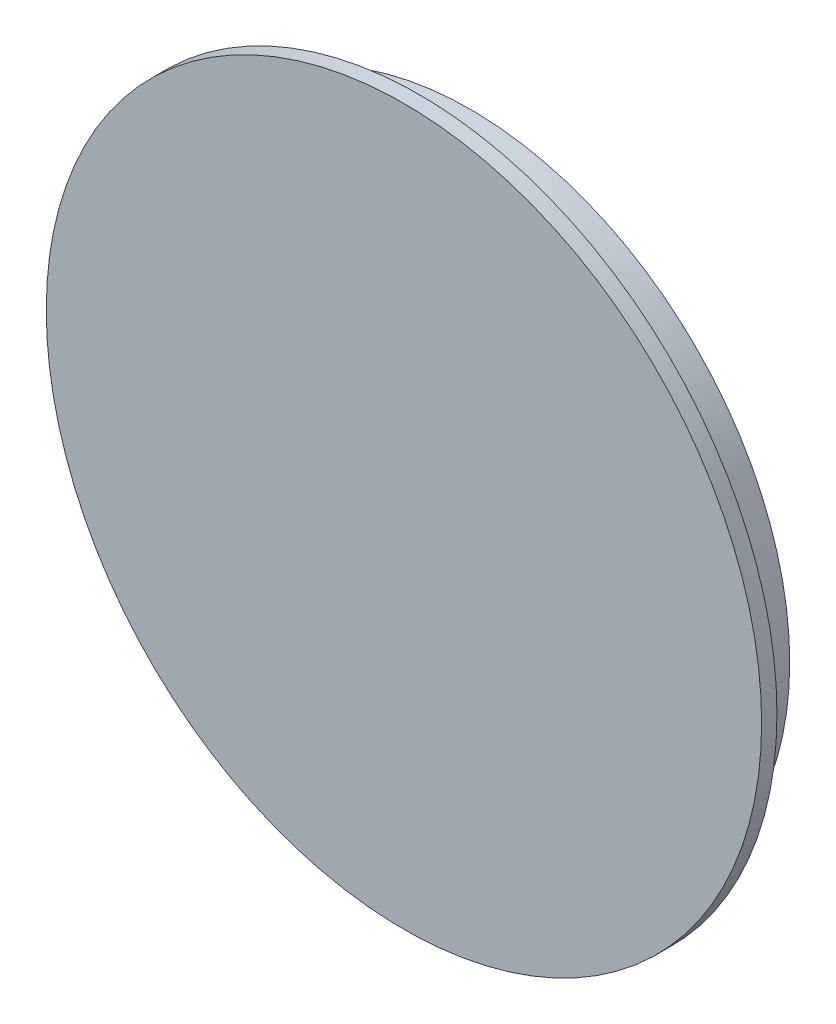
SolidWorks part; units mm, degrees
ref_plane "Front Plane" through (0, 0, 0) normal (0, 0, 1) x (1, 0, 0)
ref_plane "Top Plane" through (0, 0, 0) normal (0, 1, 0) x (1, 0, 0)
ref_plane "Right Plane" through (0, 0, 0) normal (1, 0, 0) x (0, 0, -1)
sketch "Sketch2" plane through (0, 0, 0) normal (0, 1, 0) x (1, 0, 0)
  line L0 (0, 0) -> (-88.9, 0)
  line L1 (0, 0) -> (0, 103.0516) construction
  line L2 (-88.9, 0) -> (-88.9, 3.81)
  line L3 (-88.9, 3.81) -> (-79.375, 3.81)
  line L4 (-79.375, 3.81) -> (-79.375, 16.51)
  line L5 (-79.375, 16.51) -> (-76.2, 16.51)
  line L6 (-69.85, 16.51) -> (-69.85, 3.81)
  line L7 (-69.85, 3.81) -> (0, 3.81)
  line L8 (0, 3.81) -> (0, 0)
  line L9 (-76.2, 16.51) -> (-76.2, 6.35)
  line L10 (-76.2, 6.35) -> (-73.025, 6.35)
  line L11 (-73.025, 6.35) -> (-73.025, 16.51)
  line L12 (-73.025, 16.51) -> (-69.85, 16.51)
  dimension "D1" = 177.8
  dimension "D2" = 12.7
  dimension "D3" = 152.4
  dimension "D4" = 3.175
  dimension "D5" = 146.05
  dimension "D6" = 10.16
  dimension "D8" = 3.81
revolve "Revolve1" add sketch "Sketch2" angle 360 about L1
ref_plane "Plane1" through (0, 0, -10.16) normal (0, 0, 1) x (1, 0, 0)
